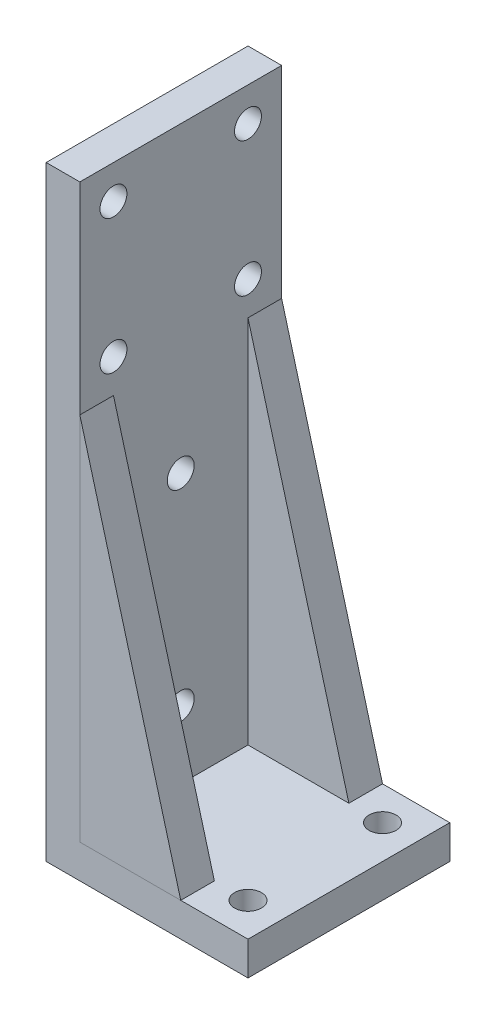
SolidWorks part; units mm, degrees
material "ABS"
ref_plane "Front Plane" through (0, 0, 0) normal (0, 0, 1) x (1, 0, 0)
ref_plane "Top Plane" through (0, 0, 0) normal (0, 1, 0) x (1, 0, 0)
ref_plane "Right Plane" through (0, 0, 0) normal (1, 0, 0) x (0, 0, -1)
sketch "Sketch1" plane through (0, 0, 0) normal (0, 1, 0) x (1, 0, 0)
  line L1 (-15, -15) -> (15, -15)
  line L2 (-15, -15) -> (-15, 15)
  line L3 (-15, 15) -> (15, 15)
  line L4 (15, -15) -> (15, 15)
  line L5 (-15, -15) -> (15, 15) construction
  line L6 (-15, 15) -> (15, -15) construction
  point P0 (0, 0)
  dimension "D1" = 30
  dimension "D2" = 30
extrude "Boss-Extrude1" add sketch "Sketch1" along normal blind 5
sketch "Sketch2" plane through (0, 5, 0) normal (0, 1, 0) x (1, 0, 0)
  line L0 (-15, -15) -> (15, -15) construction
  line L1 (-15, 15) -> (-10, 15)
  line L2 (-15, 15) -> (-15, -15)
  line L3 (-15, -15) -> (-10, -15)
  line L4 (-10, 15) -> (-10, -15)
  dimension "D1" = 5
extrude "Boss-Extrude2" add sketch "Sketch2" along normal blind 85
ref_plane "Plane1" through (0, 0, 15) normal (0, 0, 1) x (1, 0, 0)
sketch "Sketch3" plane through (0, 0, 15) normal (0, 0, 1) x (1, 0, 0)
  line L0 (-10, 5) -> (-10, 60)
  line L1 (-10, 90) -> (-10, 5) construction
  line L2 (-10, 60) -> (5, 5)
  line L3 (-10, 5) -> (15, 5) construction
  line L4 (5, 5) -> (-10, 5)
  dimension "D1" = 55
  dimension "D2" = 15
extrude "Boss-Extrude3" add sketch "Sketch3" against normal blind 5 separate body
ref_plane "Plane2" through (0, 0, -15) normal (0, 0, 1) x (1, 0, 0)
sketch "Sketch5" plane through (0, 0, -15) normal (0, 0, 1) x (1, 0, 0)
  line L0 (-10, 5) -> (-10, 60)
  line L1 (-10, 90) -> (-10, 5) construction
  line L2 (5, 5) -> (-10, 60) construction
  line L3 (-10, 60) -> (5, 5)
  line L4 (15, 5) -> (-10, 5) construction
  line L5 (5, 5) -> (-10, 5)
  dimension "D1" = 15
extrude "Boss-Extrude4" add sketch "Sketch5" along normal blind 5
sketch "Sketch10" plane through (-10, 0, 0) normal (1, 0, 0) x (0, 0, -1)
  line L0 (-15, 90) -> (-15, 5) construction
  line L1 (-15, 90) -> (15, 90) construction
  line L2 (15, 90) -> (15, 60) construction
  line L3 (-15, 90) -> (-15, 0) construction
  line L4 (15, 0) -> (-15, 0) construction
  circle A0 centre (-10, 85) radius 2
  circle A1 centre (10, 85) radius 2
  circle A2 centre (0, 15) radius 2
  circle A3 centre (0, 45) radius 2
  dimension "D1" = 4
  dimension "D4" = 4
  dimension "D7" = 4
  dimension "D8" = 4
  dimension "D2" = 5
  dimension "D3" = 5
  dimension "D5" = 5
  dimension "D6" = 5
  dimension "D9" = 15
  dimension "D10" = 15
  dimension "D11" = 15
  dimension "D12" = 45
extrude "Cut-Extrude1" cut sketch "Sketch10" against normal blind 5
sketch "Sketch11" plane through (0, 5, 0) normal (0, 1, 0) x (1, 0, 0)
  line L0 (15, -15) -> (15, 15) construction
  line L1 (15, 15) -> (5, 15) construction
  line L2 (-10, -15) -> (15, -15) construction
  circle A0 centre (10, 10) radius 2
  circle A1 centre (10, -10) radius 2
  dimension "D1" = 4
  dimension "D4" = 4
  dimension "D2" = 5
  dimension "D3" = 5
  dimension "D5" = 5
  dimension "D6" = 5
extrude "Cut-Extrude2" cut sketch "Sketch11" against normal blind 5
sketch "Sketch12" plane through (-10, 0, 0) normal (1, 0, 0) x (0, 0, -1)
  line L0 (-15, 90) -> (-15, 5) construction
  line L1 (-10, 60) -> (-15, 60) construction
  line L2 (15, 90) -> (15, 60) construction
  line L3 (10, 60) -> (15, 60) construction
  circle A0 centre (-10, 65) radius 2
  circle A1 centre (10, 65) radius 2
  dimension "D1" = 4
  dimension "D2" = 4
  dimension "D3" = 5
  dimension "D4" = 5
  dimension "D5" = 5
  dimension "D6" = 5
extrude "Cut-Extrude3" cut sketch "Sketch12" against normal blind 5
